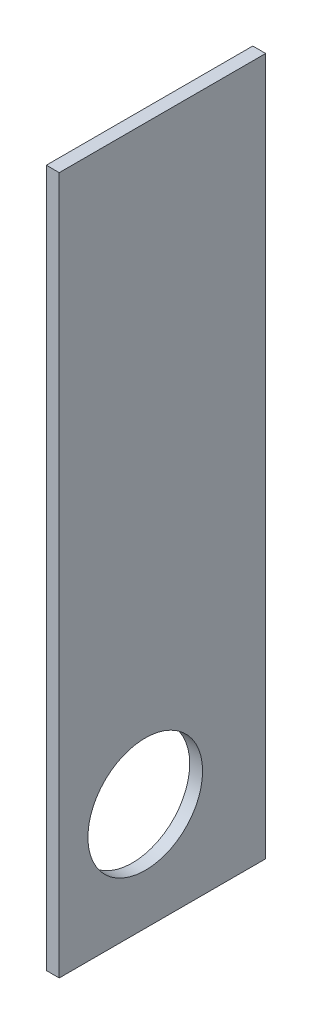
SolidWorks part; units mm, degrees
ref_plane "Front Plane" through (0, 0, 0) normal (0, 0, 1) x (1, 0, 0)
ref_plane "Top Plane" through (0, 0, 0) normal (0, 1, 0) x (1, 0, 0)
ref_plane "Right Plane" through (0, 0, 0) normal (1, 0, 0) x (0, 0, -1)
sketch "Sketch1" plane through (0, 0, 0) normal (1, 0, 0) x (0, 0, -1)
  line L1 (20.3921, -915.2196) -> (-267.6079, -915.2196)
  line L2 (20.3921, -915.2196) -> (20.3921, 57.7804)
  line L3 (20.3921, 57.7804) -> (-267.6079, 57.7804)
  line L4 (-267.6079, -915.2196) -> (-267.6079, -836.1219)
  line L5 (20.3921, -915.2196) -> (-267.6079, 57.7804) construction
  line L6 (20.3921, 57.7804) -> (-267.6079, -915.2196) construction
  line L7 (-267.6079, -676.1219) -> (-267.6079, 57.7804)
  line L10 (-267.6079, -676.1219) -> (-267.6079, -836.1219)
  circle A0 centre (-147.6079, -765.2196) radius 80
  point P0 (-123.6079, -428.7196)
  dimension "D3" = 160
  dimension "D4" = 120
  dimension "D1" = 288
  dimension "D2" = 973
  dimension "D5" = 150
extrude "Boss-Extrude1" add sketch "Sketch1" along normal blind 18
equation "\"H_POLKI\"=973"
equation "\"D2@Sketch1\"=\"H_POLKI\""
equation "\"DSP_WIDTH\"=18"
equation "\"D1@Boss-Extrude1\"=\"DSP_WIDTH\""
